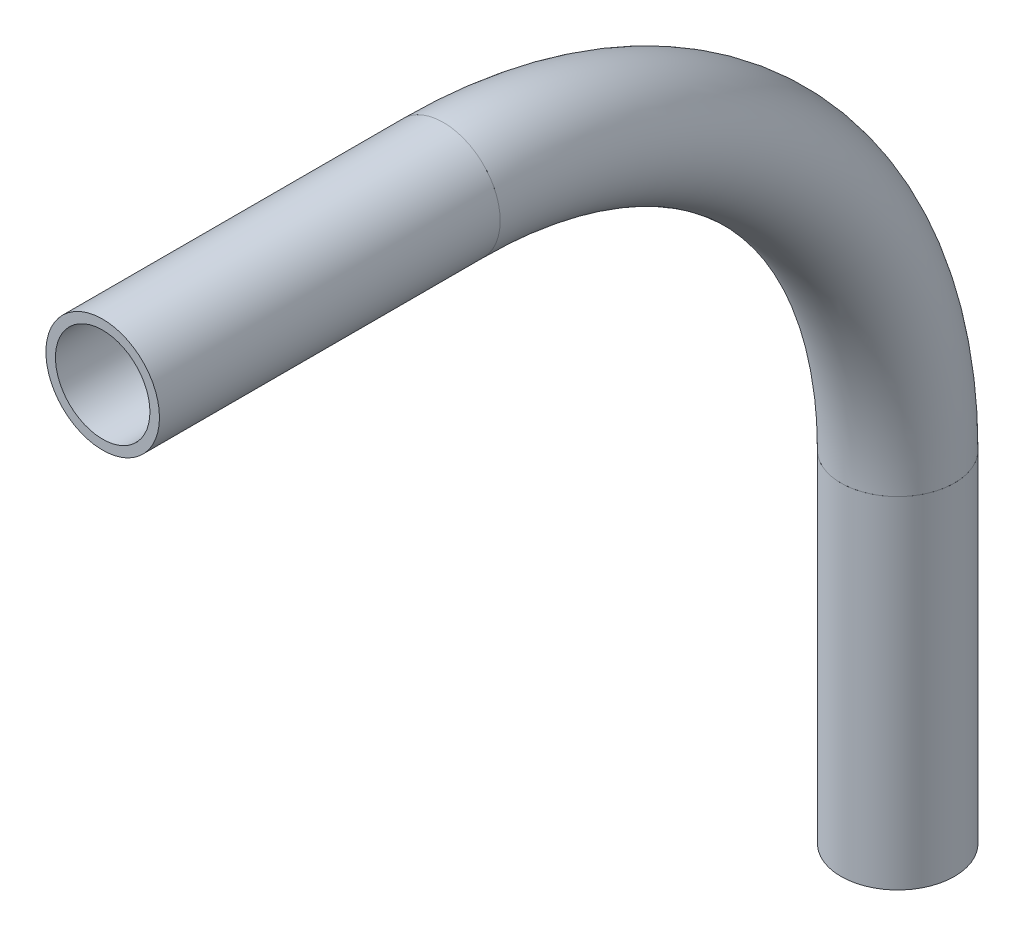
SolidWorks part; units mm, degrees
ref_plane "Front Plane" through (0, 0, 0) normal (0, 0, 1) x (1, 0, 0)
ref_plane "Top Plane" through (0, 0, 0) normal (0, 1, 0) x (1, 0, 0)
ref_plane "Right Plane" through (0, 0, 0) normal (1, 0, 0) x (0, 0, -1)
sketch "Sketch1" plane through (0, 0, 0) normal (1, 0, 0) x (0, 0, -1)
  line L0 (-363.5712, -256.5245) -> (-325.4712, -256.5245)
  line L2 (-274.6712, -307.3245) -> (-274.6712, -345.4245)
  arc A0 (-325.4712, -256.5245) -> (-274.6712, -307.3245) centre (-325.4712, -307.3245) cw
  dimension "D1" = 50.8
  dimension "D2" = 38.1
  dimension "D3" = 38.1
other "Pipe 0.5 SCH 40(1)"
ref_plane "Plane1" through (0, -307.3245, 274.6712) normal (0, -1, 0) x (0, 0, -1)
sketch "Sketch11" plane through (0, -307.3245, 274.6712) normal (0, -1, 0) x (0, 0, -1)
  circle A0 centre (0, 0) radius 5.2832
  circle A1 centre (0, 0) radius 6.35
  point P5 (0, 0)
  dimension "In_dia" = 10.5664
  dimension "Out_dia" = 12.7
